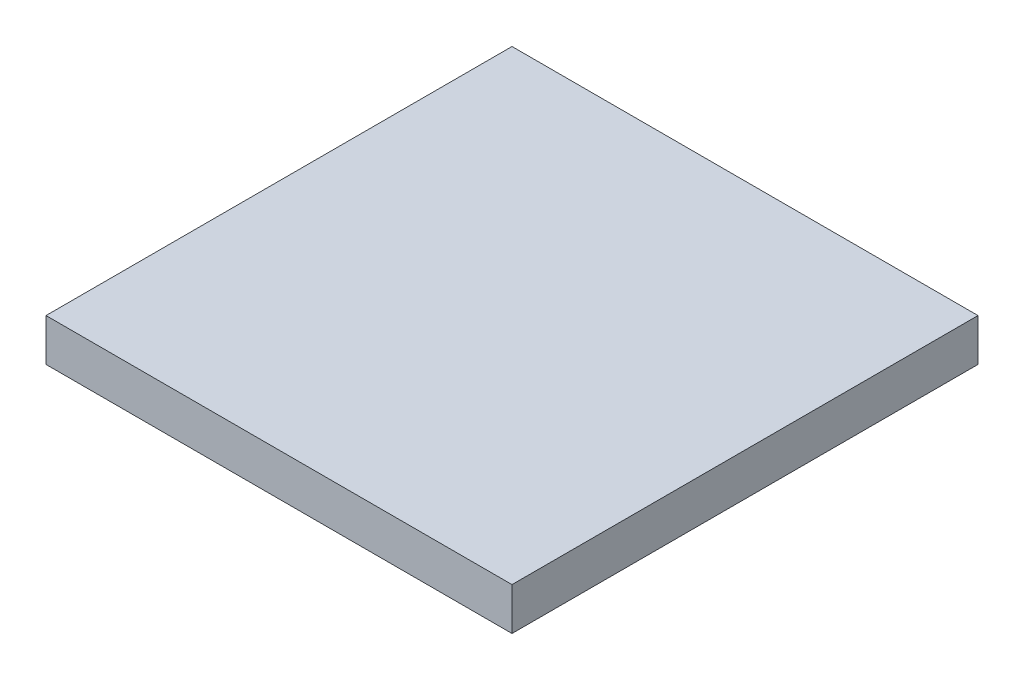
SolidWorks part; units mm, degrees
material "Beech"
ref_plane "Plane1" through (0, 0, 0) normal (0, 0, 1) x (1, 0, 0)
ref_plane "Plane2" through (0, 0, 0) normal (0, 1, 0) x (1, 0, 0)
ref_plane "Plane3" through (0, 0, 0) normal (1, 0, 0) x (0, 0, -1)
sketch "Sketch1" plane through (0, 0, 0) normal (0, 1, 0) x (1, 0, 0)
  line L1 (0, 0) -> (550, 0)
  line L2 (0, 0) -> (0, 550)
  line L3 (0, 550) -> (550, 550)
  line L4 (550, 0) -> (550, 550)
  dimension "D1" = 550
  dimension "D2" = 550
extrude "Boss-Extrude1" add sketch "Sketch1" along normal blind 50
